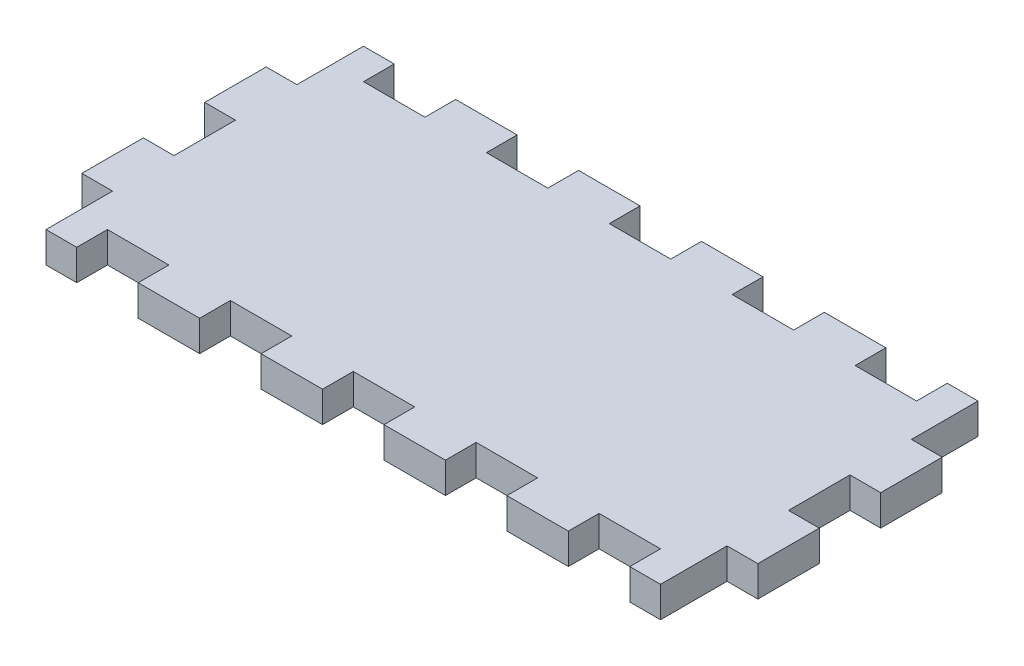
SolidWorks part; units mm, degrees
ref_plane "Front Plane" through (0, 0, 0) normal (0, 0, 1) x (1, 0, 0)
ref_plane "Top Plane" through (0, 0, 0) normal (0, 1, 0) x (1, 0, 0)
ref_plane "Right Plane" through (0, 0, 0) normal (1, 0, 0) x (0, 0, -1)
sketch "Sketch1" plane through (0, 0, 0) normal (0, 1, 0) x (1, 0, 0)
  line L0 (-60, -18) -> (-66, -18)
  line L1 (-54, -25) -> (-42, -25)
  line L2 (-60, -25) -> (-60, -18)
  line L3 (-54, 25) -> (-42, 25)
  line L4 (60, -25) -> (60, -18)
  line L5 (-6, -25) -> (6, -25)
  line L7 (-66, -18) -> (-66, -6)
  line L8 (-66, -6) -> (-60, -6)
  line L9 (-60, 6) -> (-66, 6)
  line L10 (-66, 6) -> (-66, 18)
  line L11 (-66, 18) -> (-60, 18)
  line L12 (0, -55) -> (0, 55) construction
  line L13 (66, 18) -> (60, 18)
  line L14 (66, 6) -> (66, 18)
  line L15 (60, 6) -> (66, 6)
  line L16 (66, -6) -> (60, -6)
  line L17 (66, -18) -> (66, -6)
  line L18 (60, -18) -> (66, -18)
  line L19 (-60, 25) -> (-60, 31)
  line L20 (-60, 31) -> (-54, 31)
  line L21 (-54, 31) -> (-54, 25)
  line L22 (-42, 25) -> (-42, 31)
  line L23 (-42, 31) -> (-30, 31)
  line L24 (-30, 31) -> (-30, 25)
  line L25 (-18, 25) -> (-18, 31)
  line L26 (-18, 31) -> (-6, 31)
  line L27 (-6, 31) -> (-6, 25)
  line L28 (6, 25) -> (6, 31)
  line L29 (6, 31) -> (18, 31)
  line L30 (18, 31) -> (18, 25)
  line L31 (60, 25) -> (60, 31)
  line L32 (60, 31) -> (54, 31)
  line L33 (54, 31) -> (54, 25)
  line L34 (-54, 31) -> (-42, 31) construction
  line L35 (-30, 31) -> (-18, 31) construction
  line L36 (-6, 31) -> (6, 31) construction
  line L37 (30, 25) -> (30, 31)
  line L38 (30, 31) -> (42, 31)
  line L39 (42, 31) -> (42, 25)
  line L40 (30, 31) -> (18, 31) construction
  line L41 (-55, 0) -> (55, 0) construction
  line L42 (30, -31) -> (18, -31) construction
  line L43 (-6, -31) -> (6, -31) construction
  line L44 (-30, -31) -> (-18, -31) construction
  line L45 (-54, -31) -> (-42, -31) construction
  line L46 (42, -31) -> (42, -25)
  line L47 (30, -31) -> (42, -31)
  line L48 (30, -25) -> (30, -31)
  line L49 (54, -31) -> (54, -25)
  line L50 (60, -31) -> (54, -31)
  line L51 (60, -25) -> (60, -31)
  line L52 (18, -31) -> (18, -25)
  line L53 (6, -31) -> (18, -31)
  line L54 (6, -25) -> (6, -31)
  line L55 (-6, -31) -> (-6, -25)
  line L56 (-18, -31) -> (-6, -31)
  line L57 (-18, -25) -> (-18, -31)
  line L58 (-30, -31) -> (-30, -25)
  line L59 (-42, -31) -> (-30, -31)
  line L60 (-42, -25) -> (-42, -31)
  line L61 (-54, -31) -> (-54, -25)
  line L62 (-60, -31) -> (-54, -31)
  line L63 (-60, -25) -> (-60, -31)
  line L64 (-60, -6) -> (-60, 6)
  line L65 (-60, 18) -> (-60, 25)
  line L66 (-30, 25) -> (-18, 25)
  line L67 (-6, 25) -> (6, 25)
  line L68 (18, 25) -> (30, 25)
  line L69 (42, 25) -> (54, 25)
  line L70 (60, 18) -> (60, 25)
  line L71 (60, -6) -> (60, 6)
  line L72 (42, -25) -> (54, -25)
  line L73 (18, -25) -> (30, -25)
  line L74 (-30, -25) -> (-18, -25)
  point P0 (0, 0)
  point P46 (42.3971, 31)
  dimension "D1" = 50
  dimension "D2" = 120
  dimension "D3" = 12
  dimension "D4" = 7
  dimension "D5" = 6
  dimension "D7" = 6
  dimension "D8" = 6
  dimension "D9" = 12
  dimension "D10" = 12
  dimension "D6" = 2
extrude "Boss-Extrude1" add sketch "Sketch1" along normal blind 6 contours L58 L74 L54 L53 L52 L73 L48 L47 L46 L72 L49 L50 L51 L4 L18 L17 L16 L71 L15 L14 L13 L70 L31 L32 L33 L69 L39 L38 L37 L68 L30 L29 L28 L67 L27 L26 L25 L66 L24 L23 L22 L3 L21 L20 L19 L65 L11 L10 L9
